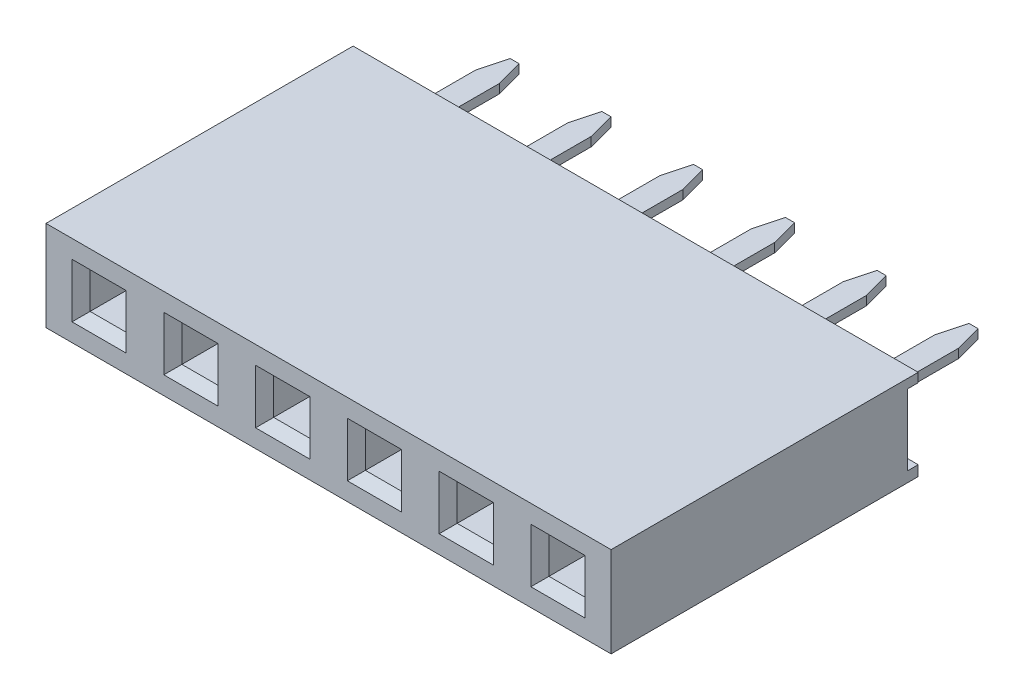
SolidWorks part; units mm, degrees
ref_plane "Front Plane" through (0, 0, 0) normal (0, 0, 1) x (1, 0, 0)
ref_plane "Top Plane" through (0, 0, 0) normal (0, 1, 0) x (1, 0, 0)
ref_plane "Right Plane" through (0, 0, 0) normal (1, 0, 0) x (0, 0, -1)
sketch "Sketch1" plane through (0, 0, 0) normal (0, 0, 1) x (1, 0, 0)
  line L1 (0, 0) -> (15.64, 0)
  line L2 (0, 0) -> (0, 2.5)
  line L3 (0, 2.5) -> (15.64, 2.5)
  line L4 (15.64, 0) -> (15.64, 2.5)
  dimension "width" = 2.5
  dimension "length" = 15.64
extrude "Boss-Extrude1" add sketch "Sketch1" along normal blind 8.5
sketch "Sketch2" plane through (0, 0, 8.5) normal (0, 0, 1) x (1, 0, 0)
  line L0 (0, 1.25) -> (15.64, 1.25) construction
  line L1 (0, 2.5) -> (0, 0) construction
  line L2 (15.64, 0) -> (15.64, 2.5) construction
  line L3 (0, 0) -> (15.64, 0) construction
  line L5 (15.64, 2.5) -> (0, 2.5) construction
  line L6 (1.47, 2.5) -> (1.47, 0) construction
  line L7 (0.97, 1.75) -> (1.97, 1.75)
  line L8 (0.97, 1.75) -> (0.97, 0.75)
  line L9 (0.97, 0.75) -> (1.97, 0.75)
  line L10 (1.97, 1.75) -> (1.97, 0.75)
  point P16 (1.47, 1.75)
  point P17 (1.97, 1.25)
  dimension "D1" = 1.25
  dimension "D2" = 1.47
  dimension "D3" = 1
  dimension "D4" = 1
extrude "Cut-Extrude1" cut sketch "Sketch2" against normal blind 2.25
chamfer "Chamfer1" distance 0.25 angle 45 4 edges at (0.97, 1.25, 8.5) (1.47, 0.75, 8.5) (1.97, 1.25, 8.5) (1.47, 1.75, 8.5)
sketch "Sketch3" plane through (0, 0, 0) normal (-1, 0, 0) x (0, 0, 1)
  line L0 (0, 2.5) -> (0, 0) construction
  line L1 (0, 2.25) -> (0.3, 2.25)
  line L2 (0, 2.25) -> (0, 0.2861)
  line L3 (0, 0.2861) -> (0.3, 0.2861)
  line L4 (0.3, 2.25) -> (0.3, 0.2861)
  line L5 (8.5, 1.25) -> (0, 1.2681) construction
  line L6 (8.5, 2.5) -> (0, 2.5) construction
  line L7 (8.5, 2.5) -> (8.5, 0) construction
  dimension "D1" = 0.25
  dimension "D2" = 0.3
extrude "Cut-Extrude2" cut sketch "Sketch3" against normal through all
ref_plane "Plane1" through (0, 1.25, 0) normal (0, -1, 0) x (-1, 0, 0)
sketch "Sketch4" plane through (0, 1.25, 0) normal (0, -1, 0) x (-1, 0, 0)
  line L0 (-1.47, -8.25) -> (-1.47, -0.3) construction
  line L1 (-0.97, -8.25) -> (-1.97, -8.25) construction
  line L2 (-15.64, -0.3) -> (0, -0.3) construction
  line L3 (0, 0) -> (-15.64, 0) construction
  line L4 (-1.795, -0.3) -> (-1.145, -0.3)
  line L5 (-1.795, -0.3) -> (-1.795, 3)
  line L6 (-1.795, 3) -> (-1.145, 3)
  line L7 (-1.145, -0.3) -> (-1.145, 3)
  point P10 (-1.47, -0.3)
  dimension "D1" = 0.65
  dimension "D2" = 3
extrude "Boss-Extrude2" add sketch "Sketch4" along normal mid plane 0.25 separate body
chamfer "Chamfer2" distance 0.2 angle 75 2 edges at (1.145, 1.25, -3) (1.795, 1.25, -3)
pattern_linear "LPattern4" count 6 spacing 2.54 along (1, 0, 0) of bodies 104
pattern_linear "LPattern5" count 6 spacing 2.54 along (1, 0, 0) of "Cut-Extrude1", "Chamfer1"
equation "\"pins\"= 6"
equation "\"rows\" = 1"
equation "\"length\"= 2.54 * \"pins\" + .4"
equation "\"width\"= 2.5 * \"rows\""
equation "\"width@Sketch1\"= 2.5 * \"rows\""
equation "\"length@Sketch1\"= 2.54 * \"pins\" + .4"
equation "\"D2@LPattern5\"= \"rows\""
equation "\"D2@LPattern4\"= \"rows\""
equation "\"D1@LPattern4\"= \"pins\""
equation "\"D1@LPattern5\"= \"pins\""
